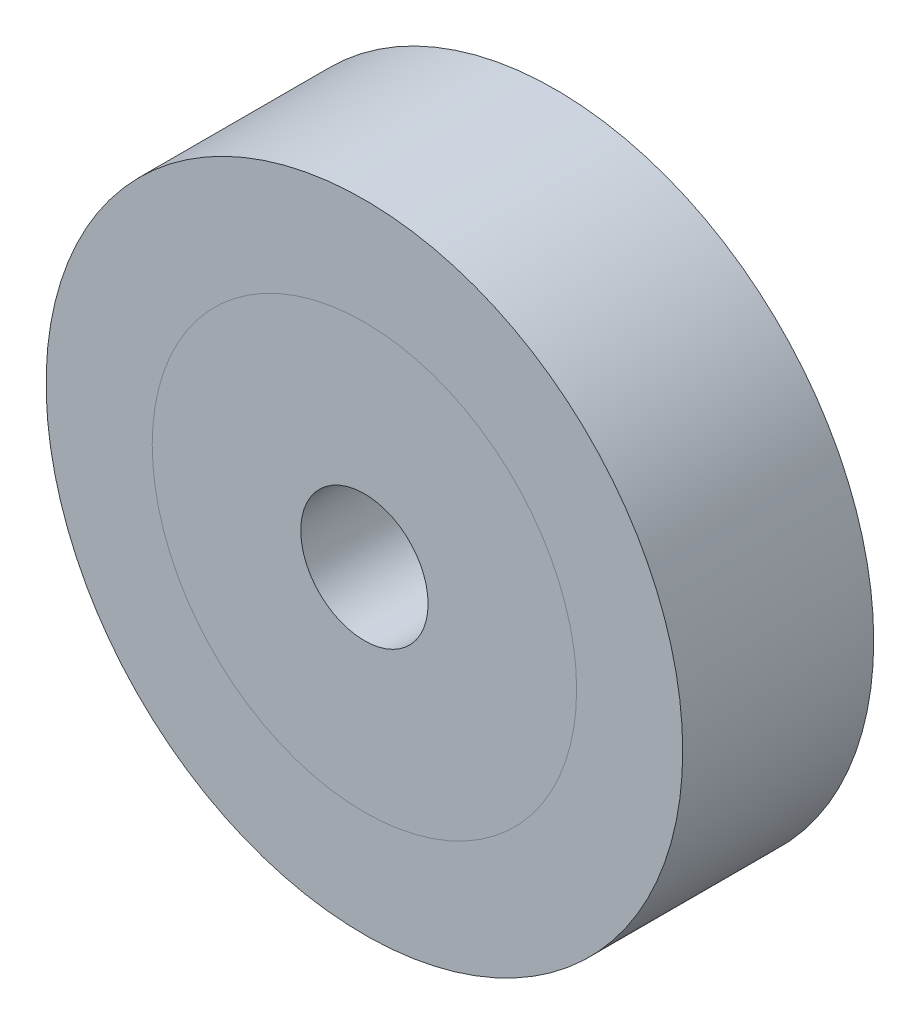
SolidWorks part; units mm, degrees
material "刚性聚氨酯泡沫体"
ref_plane "前视基准面" through (0, 0, 0) normal (0, 0, 1) x (1, 0, 0)
ref_plane "上视基准面" through (0, 0, 0) normal (0, 1, 0) x (1, 0, 0)
ref_plane "右视基准面" through (0, 0, 0) normal (1, 0, 0) x (0, 0, -1)
sketch "草图1" plane through (0, 0, 0) normal (0, 0, 1) x (1, 0, 0)
  circle A0 centre (0, 0) radius 3
  circle A1 centre (0, 0) radius 15
  dimension "D1" = 6
  dimension "D2" = 30
extrude "凸台-拉伸1" add sketch "草图1" along normal mid plane 9
sketch "草图2" plane through (0, 0, 4.5) normal (0, 0, 1) x (1, 0, 0)
  circle A0 centre (0, 0) radius 10
  dimension "D1" = 20
split line "分割线1"
